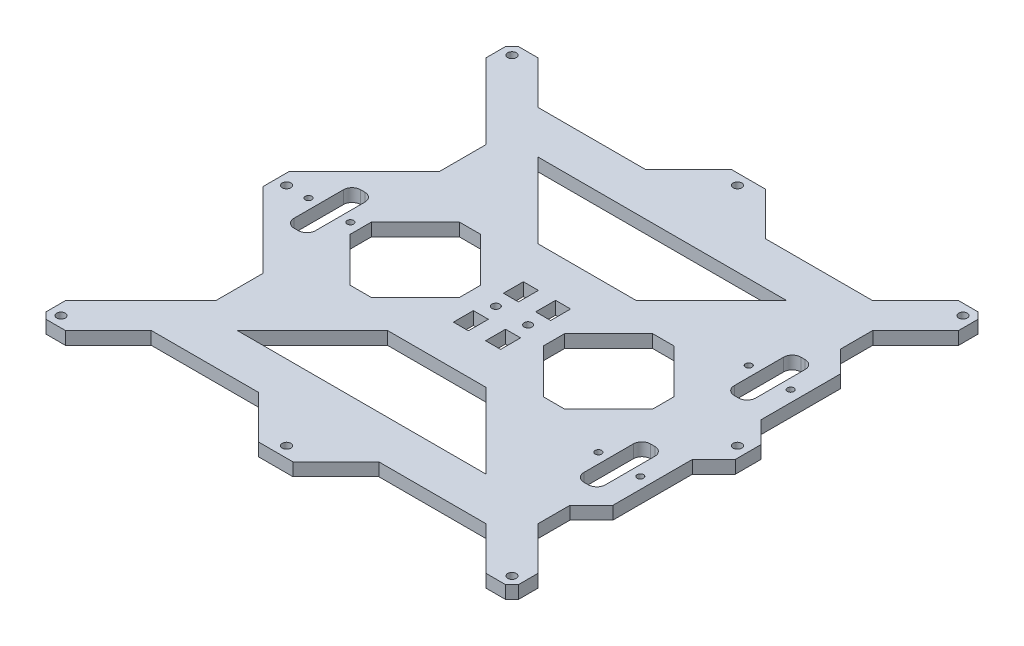
SolidWorks part; units mm, degrees
ref_plane "Plan de face" through (0, 0, 0) normal (0, 0, 1) x (1, 0, 0)
ref_plane "Plan de dessus" through (0, 0, 0) normal (0, 1, 0) x (1, 0, 0)
ref_plane "Plan de droite" through (0, 0, 0) normal (1, 0, 0) x (0, 0, -1)
sketch "Esquisse1" plane through (0, 0, 0) normal (0, 1, 0) x (1, 0, 0)
  line L0 (0, 0) -> (0, 110)
  line L1 (0, 110) -> (-8, 110)
  line L2 (-8, 110) -> (-28, 90)
  line L3 (-28, 90) -> (-78, 90)
  line L4 (-78, 90) -> (-98, 110)
  line L5 (-98, 110) -> (-110, 110)
  line L6 (-110, 110) -> (-110, 98)
  line L7 (-110, 98) -> (-75, 63)
  line L8 (-75, 63) -> (-75, 41)
  line L9 (-75, 41) -> (-110, 6)
  line L10 (-110, 6) -> (-110, 0)
  line L11 (-110, 0) -> (0, 0)
  line L12 (-8, 110) -> (-35.1818, 110) construction
  dimension "D1" = 110
  dimension "D2" = 110
  dimension "D3" = 20
  dimension "D4" = 45
  dimension "D5" = 50
  dimension "D6" = 12
  dimension "D7" = 35
  dimension "D8" = 22
extrude "Boss.-Extru.1" add sketch "Esquisse1" along normal blind 6
sketch "Esquisse3" plane through (0, 0, 0) normal (0, 1, 0) x (1, 0, 0)
  line L0 (0, 70) -> (-58, 70)
  line L1 (0, 0) -> (0, 110) construction
  line L2 (-58, 70) -> (-23, 35)
  line L3 (-23, 35) -> (0, 35)
  line L4 (-78, 90) -> (-98, 110) construction
  line L5 (-28, 90) -> (-78, 90) construction
  line L6 (-110, 0) -> (0, 0) construction
  line L7 (0, 70) -> (0, 35)
  dimension "D1" = 20
  dimension "D2" = 35
extrude "Enlèv. mat.-Extru.2" cut sketch "Esquisse3" along normal blind 6
chamfer "Chanfrein1" distance 3 angle 45 1 edges at (-110, 3, -110)
mirror "Symétrie3" about plane through (-110, 6, 0) normal (0, 0, -1) of bodies 102
sketch "Esquisse4" plane through (0, 6, 0) normal (0, 1, 0) x (1, 0, 0)
  line L0 (-7.5, 35) -> (-7.5, -35) construction
  line L1 (-23, 35) -> (0, 35) construction
  line L2 (-23, -35) -> (0, -35) construction
  line L3 (0, -35) -> (0, 35) construction
  line L4 (-7.5, 0) -> (-110, 0) construction
  line L5 (-110, 6) -> (-110, -6) construction
  line L7 (-45, 30.4056) -> (-14.5944, 0)
  line L8 (-45, 30.4056) -> (-75.4056, 0)
  line L9 (-75.4056, 0) -> (-45, -30.4056)
  line L10 (-14.5944, 0) -> (-45, -30.4056)
  line L11 (-45, 30.4056) -> (-45, -30.4056) construction
  line L12 (-75.4056, 0) -> (-14.5944, 0) construction
  point P12 (-45, 0)
  line B0 (-4, 16.3) -> (-4, 7)
  line B1 (-4, 16.3) -> (-11, 16.3)
  line B2 (-11, 16.3) -> (-11, 7)
  line B3 (-4, 7) -> (-11, 7)
  line B4 (-4, -7) -> (-11, -7)
  line B5 (-11, -16.3) -> (-11, -7)
  line B6 (-4, -16.3) -> (-11, -16.3)
  line B7 (-4, -16.3) -> (-4, -7)
  circle B8 centre (-7.5, 0) radius 1.8
  dimension "D1" = 7.5
  dimension "D2" = 65
  dimension "D3" = 43
sketch_block_instance "attache_femelle-1"
sketch_block "attache_femelle" parameters "D1"=3.6, "D2"=9.3, "D3"=7, "D4"=7
extrude "Enlèv. mat.-Extru.3" cut sketch "Esquisse4" against normal blind 6
chamfer "Chanfrein2" distance 7 angle 45 4 edges at (-45, 3, 30.4056) (-14.5944, 3, 0) (-45, 3, -30.4056) (-75.4056, 3, 0)
mirror "Symétrie5" about plane through (0, 6, 0) normal (-1, 0, 0) of bodies 106
sketch "Esquisse8" plane through (0, 6, 0) normal (0, 1, 0) x (1, 0, 0)
  line L0 (100, 16) -> (100, 53)
  line L1 (75, 41) -> (110, 6) construction
  line L2 (100, 53) -> (90, 63)
  line L3 (90, 63) -> (90, 78)
  line L4 (110, 98) -> (75, 63) construction
  line L5 (90, 78) -> (75, 63)
  line L6 (75, 63) -> (75, 41)
  line L7 (75, 41) -> (100, 16)
  dimension "D1" = 10
  dimension "D2" = 15
  dimension "D3" = 10
extrude "Boss.-Extru.2" add sketch "Esquisse8" against normal blind 6
sketch "Esquisse11" plane through (0, 6, 0) normal (0, 1, 0) x (1, 0, 0)
  line L0 (-105, 105) -> (105, 105) construction
  line L1 (105, 105) -> (105, -105) construction
  line L2 (105, -105) -> (-105, -105) construction
  line L3 (-105, -105) -> (-105, 105) construction
  line L4 (-98, 110) -> (-107, 110) construction
  line L5 (-110, 107) -> (-110, 98) construction
  line L6 (0, 105) -> (0, -105) construction
  line L7 (-105, 0) -> (105, 0) construction
  circle A0 centre (-105, 105) radius 2
  circle A1 centre (0, 105) radius 2
  circle A2 centre (105, 105) radius 2
  circle A3 centre (105, 0) radius 2
  circle A4 centre (105, -105) radius 2
  circle A5 centre (0, -105) radius 2
  circle A6 centre (-105, -105) radius 2
  circle A7 centre (-105, 0) radius 2
  dimension "D4" = 4
  dimension "D1" = 210
  dimension "D2" = 5
  dimension "D3" = 5
extrude "Enlèv. mat.-Extru.6" cut sketch "Esquisse11" against normal blind 6
mirror "Symétrie6" about plane through (0, 0, 0) normal (0, 0, 1) of "Boss.-Extru.2"
sketch "Esquisse12" plane through (0, 6, 0) normal (0, 1, 0) x (1, 0, 0)
  line L0 (85, 35) -> (85, -35) construction
  line L1 (-85, 0) -> (85, 0) construction
  line B0 (-86, 15.5) -> (-84, 15.5)
  line B1 (-90, 11.5) -> (-90, -11.5)
  line B2 (-86, -15.5) -> (-84, -15.5)
  line B3 (-80, 11.5) -> (-80, -11.5)
  circle B4 centre (-94.75, 0) radius 1.5
  circle B5 centre (-75.25, 0) radius 1.5
  arc B6 (-90, -11.5) -> (-86, -15.5) centre (-86, -11.5) ccw
  arc B7 (-84, -15.5) -> (-80, -11.5) centre (-84, -11.5) ccw
  arc B8 (-84, 15.5) -> (-80, 11.5) centre (-84, 11.5) cw
  arc B9 (-86, 15.5) -> (-90, 11.5) centre (-86, 11.5) ccw
  line B10 (84, 50.5) -> (86, 50.5)
  line B11 (80, 46.5) -> (80, 23.5)
  line B12 (84, 19.5) -> (86, 19.5)
  line B13 (90, 46.5) -> (90, 23.5)
  circle B14 centre (75.25, 35) radius 1.5
  circle B15 centre (94.75, 35) radius 1.5
  arc B16 (80, 23.5) -> (84, 19.5) centre (84, 23.5) ccw
  arc B17 (86, 19.5) -> (90, 23.5) centre (86, 23.5) ccw
  arc B18 (86, 50.5) -> (90, 46.5) centre (86, 46.5) cw
  arc B19 (84, 50.5) -> (80, 46.5) centre (84, 46.5) ccw
  line B20 (84, -19.5) -> (86, -19.5)
  line B21 (80, -23.5) -> (80, -46.5)
  line B22 (84, -50.5) -> (86, -50.5)
  line B23 (90, -23.5) -> (90, -46.5)
  circle B24 centre (75.25, -35) radius 1.5
  circle B25 centre (94.75, -35) radius 1.5
  arc B26 (80, -46.5) -> (84, -50.5) centre (84, -46.5) ccw
  arc B27 (86, -50.5) -> (90, -46.5) centre (86, -46.5) ccw
  arc B28 (86, -19.5) -> (90, -23.5) centre (86, -23.5) cw
  arc B29 (84, -19.5) -> (80, -23.5) centre (84, -23.5) ccw
  dimension "D1" = 170
  dimension "D2" = 70
sketch_block_instance "Bloc-attache_bearing-1"
sketch_block "Bloc1" parameters "D4"=3, "D5"=4, "D1"=31, "D2"=10, "D3"=19.5
sketch_block_instance "Bloc1-1"
sketch_block_instance "Bloc1-2"
extrude "Enlèv. mat.-Extru.7" cut sketch "Esquisse12" against normal blind 10
